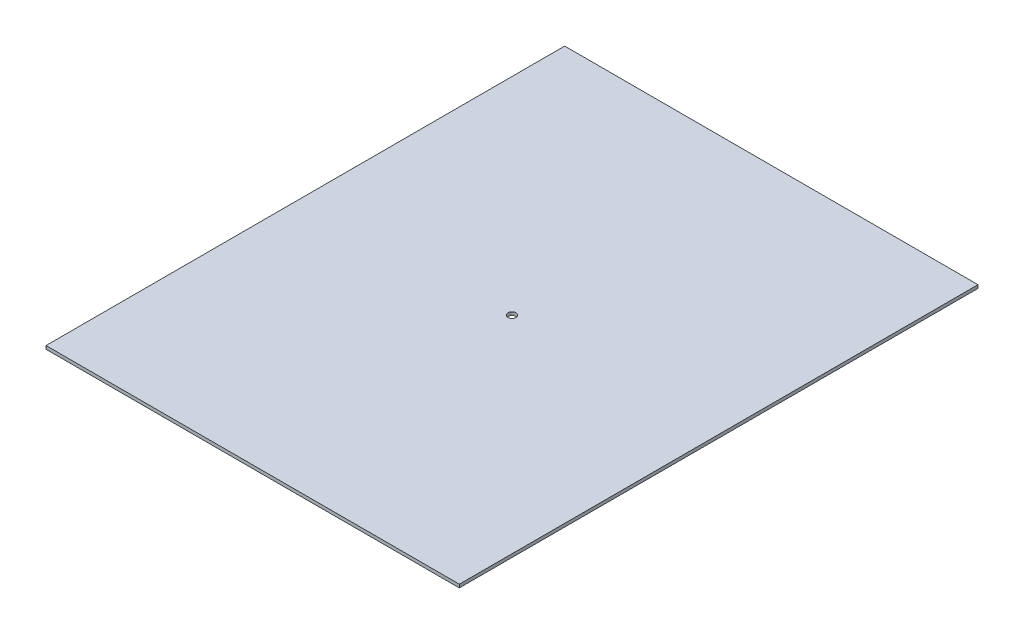
SolidWorks part; units mm, degrees
ref_plane "Front" through (0, 0, 0) normal (0, 0, 1) x (1, 0, 0)
ref_plane "Top" through (0, 0, 0) normal (0, 1, 0) x (1, 0, 0)
ref_plane "Right" through (0, 0, 0) normal (1, 0, 0) x (0, 0, -1)
sketch "Sketch1" plane through (0, 0, 0) normal (0, 1, 0) x (1, 0, 0)
  line L1 (-87.1307, 175.2344) -> (167.8693, 175.2344)
  line L2 (-87.1307, 175.2344) -> (-87.1307, -144.7656)
  line L3 (-87.1307, -144.7656) -> (167.8693, -144.7656)
  line L4 (167.8693, 175.2344) -> (167.8693, -144.7656)
  circle A0 centre (40.3693, 15.2344) radius 2.5
  dimension "D3" = 127.5
  dimension "D1" = 255
  dimension "D2" = 320
extrude "Boss-Extrude1" add sketch "Sketch1" along normal blind 2
